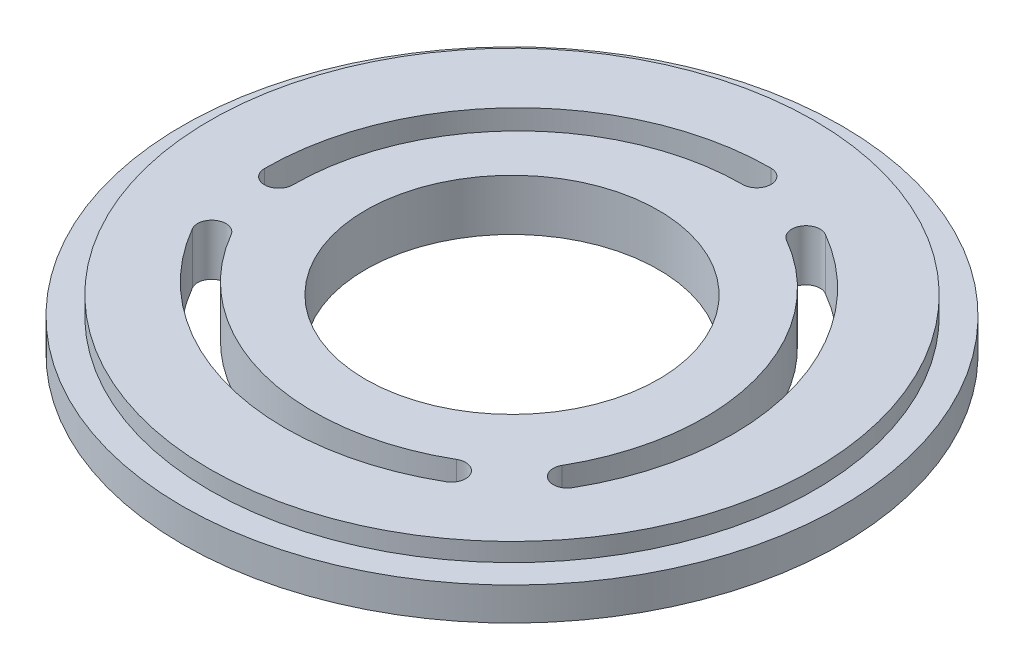
SolidWorks part; units mm, degrees
ref_plane "Front Plane" through (0, 0, 0) normal (0, 0, 1) x (1, 0, 0)
ref_plane "Top Plane" through (0, 0, 0) normal (0, 1, 0) x (1, 0, 0)
ref_plane "Right Plane" through (0, 0, 0) normal (1, 0, 0) x (0, 0, -1)
sketch "Sketch1" plane through (0, 0, 0) normal (0, 1, 0) x (1, 0, 0)
  circle A0 centre (0, 0) radius 18
  point P3 (0, 0)
extrude "Boss-Extrude2" add sketch "Sketch1" against normal blind 1.8 contours A0
sketch "Sketch2" plane through (0, 0, 0) normal (0, 1, 0) x (1, 0, 0)
  circle A0 centre (0, 0) radius 16.5
extrude "Boss-Extrude3" add sketch "Sketch2" along normal blind 1
sketch "Sketch3" plane through (0, 1, 0) normal (0, 1, 0) x (1, 0, 0)
  circle A0 centre (0, 0) radius 8
extrude "Cut-Extrude1" cut sketch "Sketch3" against normal blind 5
sketch "Sketch5" plane through (0, 1, 0) normal (0, 1, 0) x (1, 0, 0)
  arc A0 (-11.9614, -0.7829) -> (1.0771, 12.2936) centre (1.0961, -0.7639) cw construction
  arc A1 (1.0759, 13.0681) -> (-12.7359, -0.784) centre (1.0961, -0.7639) ccw
  arc A2 (1.0782, 11.5191) -> (-11.1869, -0.7818) centre (1.0961, -0.7639) ccw
  arc A3 (1.0782, 11.5191) -> (1.0759, 13.0681) centre (1.0771, 12.2936) ccw
  arc A4 (-12.7359, -0.784) -> (-11.1869, -0.7818) centre (-11.9614, -0.7829) ccw
  arc A5 (5.3027, 10.7503) -> (10.108, -7.0796) centre (-1.2096, -0.5673) cw construction
  arc A6 (10.7793, -7.4658) -> (5.689, 11.4216) centre (-1.2096, -0.5673) ccw
  arc A7 (9.4368, -6.6933) -> (4.9164, 10.0791) centre (-1.2096, -0.5673) ccw
  arc A8 (9.4368, -6.6933) -> (10.7793, -7.4658) centre (10.108, -7.0796) ccw
  arc A9 (5.689, 11.4216) -> (4.9164, 10.0791) centre (5.3027, 10.7503) ccw
  arc A10 (6.6587, -9.9674) -> (-11.1851, -5.214) centre (0.1135, 1.3312) cw construction
  arc A11 (-11.8553, -5.6022) -> (7.0469, -10.6376) centre (0.1135, 1.3312) ccw
  arc A12 (-10.515, -4.8258) -> (6.2705, -9.2973) centre (0.1135, 1.3312) ccw
  arc A13 (-10.515, -4.8258) -> (-11.8553, -5.6022) centre (-11.1851, -5.214) ccw
  arc A14 (7.0469, -10.6376) -> (6.2705, -9.2973) centre (6.6587, -9.9674) ccw
  point P3 (-8.1504, 8.4557)
  point P14 (11.3981, 2.8306)
  point P22 (-3.2477, -11.2863)
  point P27 (0, 0)
  dimension "D1" = 3
extrude "Cut-Extrude2" cut sketch "Sketch5" against normal blind 5
